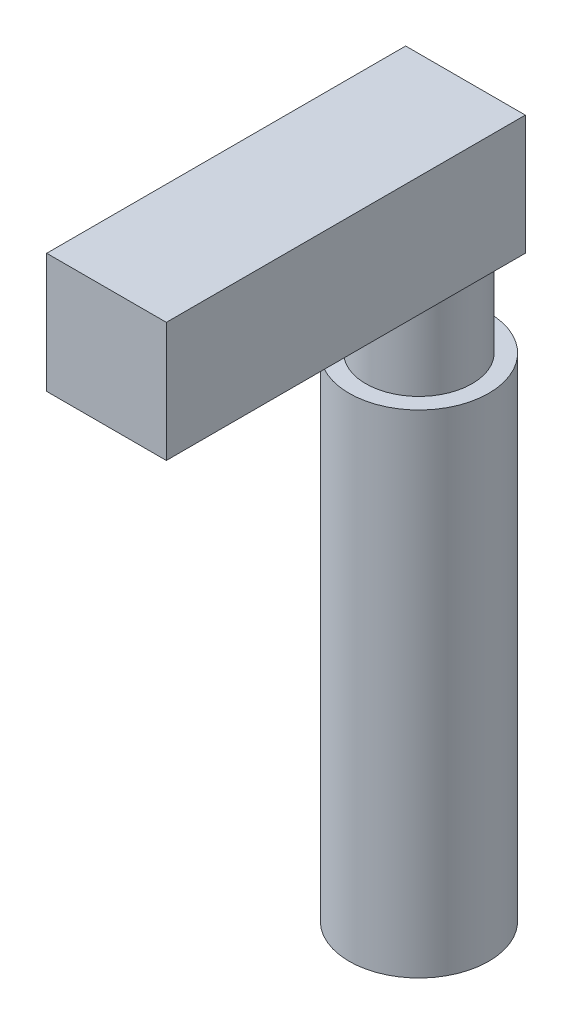
SolidWorks part; units mm, degrees
material "BUTYL"
ref_plane "前视基准面" through (0, 0, 0) normal (0, 0, 1) x (1, 0, 0)
ref_plane "上视基准面" through (0, 0, 0) normal (0, 1, 0) x (1, 0, 0)
ref_plane "右视基准面" through (0, 0, 0) normal (1, 0, 0) x (0, 0, -1)
sketch "草图1" plane through (0, 0, 0) normal (0, 0, 1) x (1, 0, 0)
  line L1 (0, 0) -> (-9, 0)
  line L2 (0, 0) -> (0, 9)
  line L3 (0, 9) -> (-9, 9)
  line L4 (-9, 0) -> (-9, 9)
  dimension "D1" = 9
  dimension "D2" = 9
extrude "凸台-拉伸1" add sketch "草图1" along normal blind 27
sketch "草图2" plane through (0, 0, 0) normal (0, -1, 0) x (1, 0, 0)
  line L0 (-9, 0) -> (0, 0) construction
  line L1 (-9, 27) -> (-9, 0) construction
  circle A0 centre (-4.5, 3.5) radius 4
  dimension "D1" = 8
  dimension "D2" = 3.5
  dimension "D3" = 4.5
extrude "凸台-拉伸2" add sketch "草图2" along normal blind 7
sketch "草图3" plane through (0, -7, 0) normal (0, -1, 0) x (1, 0, 0)
  circle A0 centre (-4.5, 3.5) radius 5.25
  dimension "D1" = 10.5
extrude "凸台-拉伸3" add sketch "草图3" along normal blind 37
